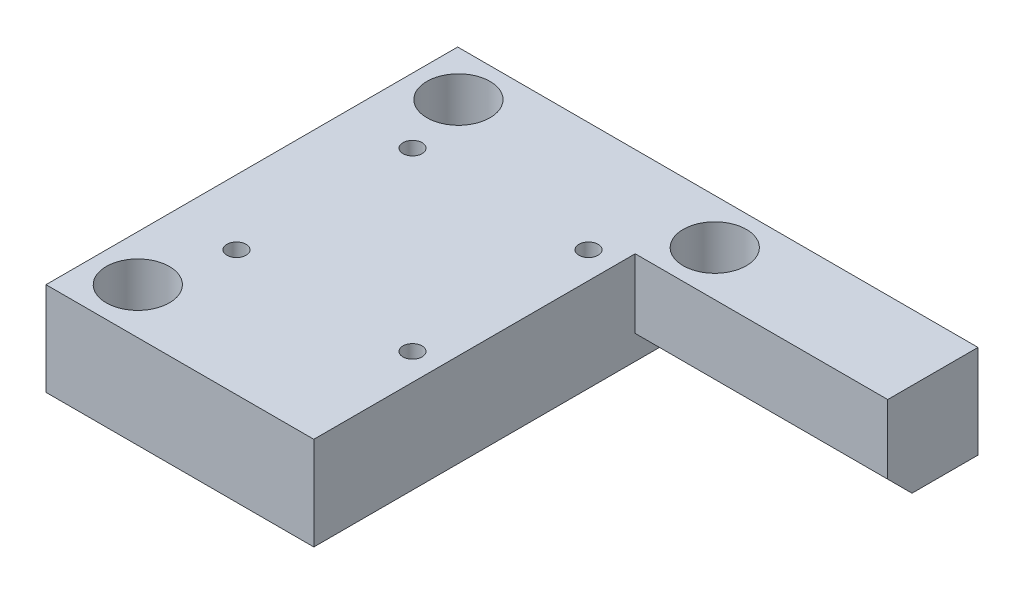
SolidWorks part; units mm, degrees
ref_plane "Front Plane" through (0, 0, 0) normal (0, 0, 1) x (1, 0, 0)
ref_plane "Top Plane" through (0, 0, 0) normal (0, 1, 0) x (1, 0, 0)
ref_plane "Right Plane" through (0, 0, 0) normal (1, 0, 0) x (0, 0, -1)
sketch "Sketch1" plane through (0, 0, 0) normal (0, 0, 1) x (1, 0, 0)
  line L1 (0, 0) -> (68, 0)
  line L2 (0, 0) -> (0, -12.192)
  line L3 (0, -12.192) -> (68, -12.192)
  line L4 (68, 0) -> (68, -12.192)
  dimension "D1" = 68
  dimension "D2" = 12.192
extrude "Boss-Extrude1" add sketch "Sketch1" along normal blind 11.8
sketch "Sketch2" plane through (0, 0, 0) normal (0, 1, 0) x (1, 0, 0)
  line L0 (68, -5.9) -> (0, -5.9) construction
  line L1 (68, -11.8) -> (68, 0) construction
  line L2 (45.5, 0) -> (45.5, -11.8) construction
  line L3 (68, 0) -> (0, 0) construction
  line L4 (68, -11.8) -> (0, -11.8) construction
  line L5 (0, -11.8) -> (0, 0) construction
  circle A0 centre (39.5, -5.9) radius 2.25
  circle A1 centre (6, -5.9) radius 2.25
  dimension "D2" = 4.5
  dimension "D3" = 4.5
  dimension "D4" = 6
  dimension "D5" = 6
  dimension "D1" = 45.5
extrude "Cut-Extrude1" cut sketch "Sketch2" against normal through all
sketch "Sketch3" plane through (0, 0, 0) normal (0, 1, 0) x (1, 0, 0)
  circle A0 centre (39.5, -5.9) radius 4.125
  circle A1 centre (6, -5.9) radius 4.125
  dimension "D1" = 8.25
  dimension "D2" = 8.25
extrude "Cut-Extrude2" cut sketch "Sketch3" against normal blind 7
sketch "Sketch4" plane through (0, 0, 11.8) normal (0, 0, 1) x (1, 0, 0)
  line L0 (0, -12.192) -> (68, -12.192) construction
  line L1 (0, 0) -> (35, 0)
  line L2 (0, 0) -> (0, -12.192)
  line L3 (0, -12.192) -> (35, -12.192)
  line L4 (35, 0) -> (35, -12.192)
  dimension "D1" = 35
extrude "Boss-Extrude2" add sketch "Sketch4" along normal blind 42
sketch "Sketch5" plane through (0, 0, 0) normal (0, 1, 0) x (1, 0, 0)
  line L0 (35, -53.8) -> (0, -53.8) construction
  line L1 (0, -53.8) -> (0, 0) construction
  circle A0 centre (6, -47.8) radius 2.25
  dimension "D1" = 4.5
  dimension "D2" = 6
  dimension "D3" = 6
extrude "Cut-Extrude3" cut sketch "Sketch5" against normal through all
sketch "Sketch6" plane through (0, 0, 0) normal (0, 1, 0) x (1, 0, 0)
  line L0 (35, -53.8) -> (0, -53.8) construction
  circle A0 centre (6, -47.8) radius 4.125
  dimension "D1" = 8.25
  dimension "D2" = 6
extrude "Cut-Extrude4" cut sketch "Sketch6" against normal blind 7
sketch "Sketch7" plane through (0, 0, 0) normal (0, 1, 0) x (1, 0, 0)
  circle A0 centre (8.5, -14.4002) radius 1.25
  circle A1 centre (8.4978, -37.4024) radius 1.25
  circle A2 centre (31.5, -37.4046) radius 1.25
  circle A3 centre (31.5022, -14.4024) radius 1.25
  dimension "D1" = 2.5
  dimension "D2" = 2.5
  dimension "D3" = 2.5
  dimension "D4" = 2.5
extrude "Cut-Extrude5" cut sketch "Sketch7" against normal up to next
chamfer "Chamfer1" distance 3.175 angle 45 1 edges
